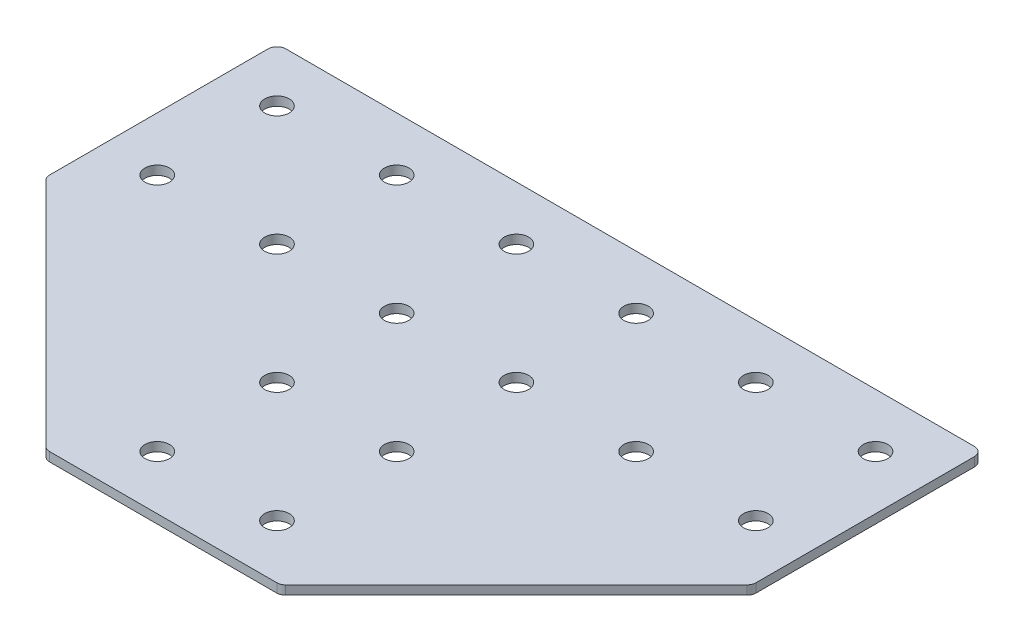
SolidWorks part; units mm, degrees
ref_plane "Спереди" through (0, 0, 0) normal (0, 0, 1) x (1, 0, 0)
ref_plane "Сверху" through (0, 0, 0) normal (0, 1, 0) x (1, 0, 0)
ref_plane "Справа" through (0, 0, 0) normal (1, 0, 0) x (0, 0, -1)
ref_plane "Плоскость1" through (0, 0.9913, 0) normal (0, -1, 0) x (1, 0, 0)
sketch "Эскиз1" plane through (0, 0.9913, 0) normal (0, -1, 0) x (1, 0, 0)
  line L0 (36.9589, 76.4791) -> (-38.8989, 76.4791)
  line L1 (-41.0203, 75.6004) -> (-118.0913, -1.4707)
  line L2 (-118.97, -3.592) -> (-118.97, -76.5209)
  line L3 (-115.97, -79.5209) -> (114.03, -79.5209)
  line L4 (117.03, -76.5209) -> (117.03, -3.592)
  line L5 (116.1513, -1.4707) -> (39.0803, 75.6004)
  arc A0 (-38.8989, 76.4791) -> (-41.0203, 75.6004) centre (-38.8989, 73.4791) ccw
  arc A1 (-118.0913, -1.4707) -> (-118.97, -3.592) centre (-115.97, -3.592) ccw
  arc A2 (-118.97, -76.5209) -> (-115.97, -79.5209) centre (-115.97, -76.5209) ccw
  arc A3 (114.03, -79.5209) -> (117.03, -76.5209) centre (114.03, -76.5209) ccw
  arc A4 (117.03, -3.592) -> (116.1513, -1.4707) centre (114.03, -3.592) ccw
  arc A5 (39.0803, 75.6004) -> (36.9589, 76.4791) centre (36.9589, 73.4791) ccw
  circle A6 centre (99.03, -21.5209) radius 4.1
  circle A7 centre (59.03, -21.5209) radius 4.1
  circle A8 centre (19.03, 58.4791) radius 4.1
  circle A9 centre (19.03, 18.4791) radius 4.1
  circle A10 centre (19.03, -21.5209) radius 4.1
  circle A11 centre (99.03, -61.5209) radius 4.1
  circle A12 centre (59.03, -61.5209) radius 4.1
  circle A13 centre (19.03, -61.5209) radius 4.1
  circle A14 centre (-100.97, -21.5209) radius 4.1
  circle A15 centre (-60.97, -21.5209) radius 4.1
  circle A16 centre (-20.97, 58.4791) radius 4.1
  circle A17 centre (-20.97, 18.4791) radius 4.1
  circle A18 centre (-20.97, -21.5209) radius 4.1
  circle A19 centre (-100.97, -61.5209) radius 4.1
  circle A20 centre (-60.97, -61.5209) radius 4.1
  circle A21 centre (-20.97, -61.5209) radius 4.1
extrude "Бобышка-Вытянуть1" add sketch "Эскиз1" against normal blind 3
